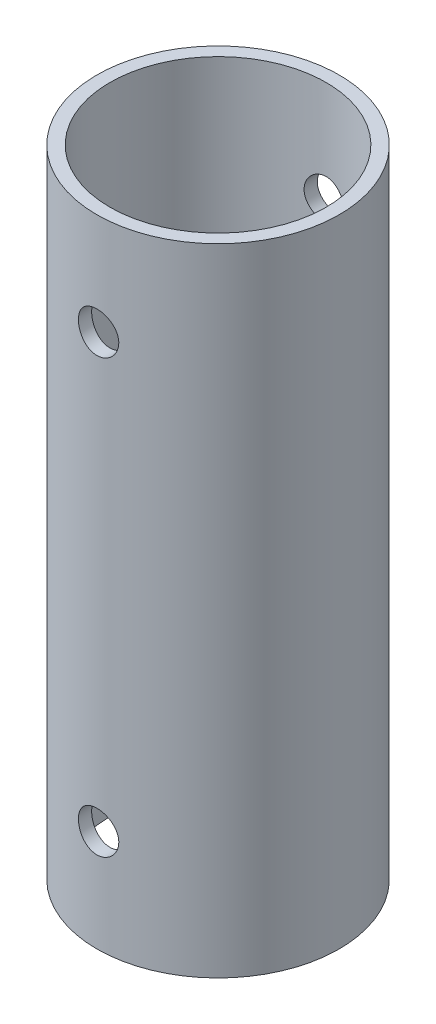
SolidWorks part; units mm, degrees
material "6061-O (SS)"
ref_plane "Alzado" through (0, 0, 0) normal (0, 0, 1) x (1, 0, 0)
ref_plane "Planta" through (0, 0, 0) normal (0, 1, 0) x (1, 0, 0)
ref_plane "Vista lateral" through (0, 0, 0) normal (1, 0, 0) x (0, 0, -1)
sketch "Croquis2" plane through (0, 0, 0) normal (0, 1, 0) x (1, 0, 0)
  circle A0 centre (0, 0) radius 9.525
  circle A1 centre (0, 0) radius 8.5
  dimension "D1" = 19.05
  dimension "D2" = 17
extrude "Saliente-Extruir1" add sketch "Croquis2" along normal blind 50
sketch "Croquis3" plane through (0, 0, 0) normal (0, 0, 1) x (1, 0, 0)
  line L0 (0, 50) -> (0, 0) construction
  line L1 (9.525, 50) -> (-9.525, 50) construction
  line L2 (-9.525, 0) -> (9.525, 0) construction
  circle A0 centre (0, 42.0025) radius 1.5875
  circle A1 centre (0, 8) radius 1.5875
  point P11 (0, 8)
  point P13 (0, 47.0875)
  point P15 (0, 6.4125)
  dimension "D2" = 6.4125
  dimension "D3" = 3.175
  dimension "D1" = 6.41
extrude "Cortar-Extruir1" cut sketch "Croquis3" against normal through all both and the other way through all
